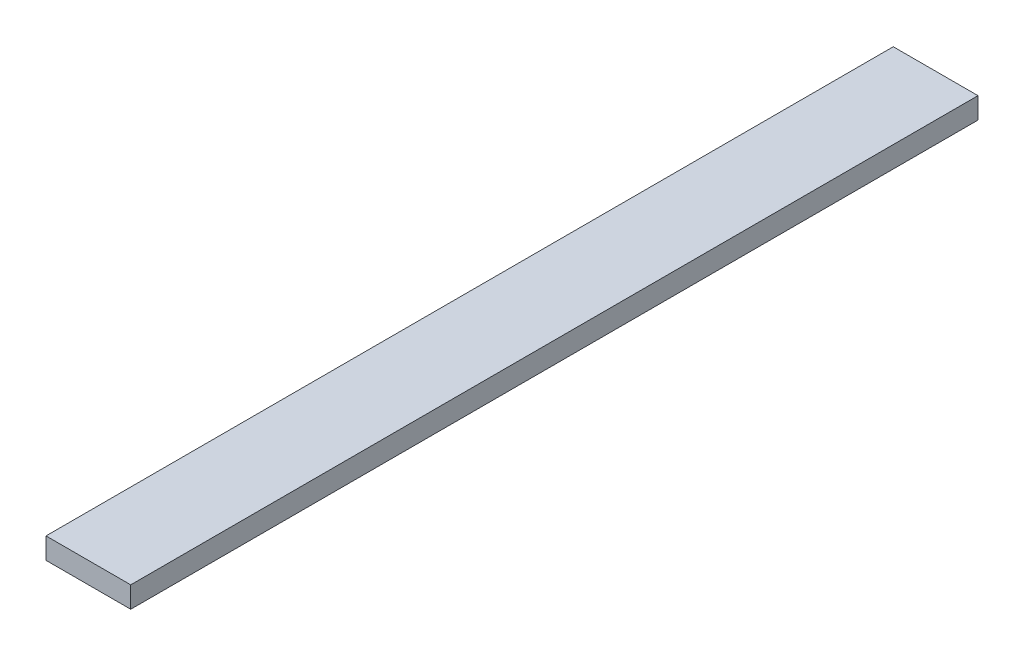
SolidWorks part; units mm, degrees
ref_plane "Front Plane" through (0, 0, 0) normal (0, 0, 1) x (1, 0, 0)
ref_plane "Top Plane" through (0, 0, 0) normal (0, 1, 0) x (1, 0, 0)
ref_plane "Right Plane" through (0, 0, 0) normal (1, 0, 0) x (0, 0, -1)
sketch "Sketch1" plane through (0, 0, 0) normal (0, 1, 0) x (1, 0, 0)
  line L1 (-3, -30) -> (3, -30)
  line L2 (-3, -30) -> (-3, 30)
  line L3 (-3, 30) -> (3, 30)
  line L4 (3, -30) -> (3, 30)
  line L5 (-3, -30) -> (3, 30) construction
  line L6 (-3, 30) -> (3, -30) construction
  point P0 (0, 0)
  dimension "D1" = 60
  dimension "D2" = 6
extrude "Boss-Extrude1" add sketch "Sketch1" along normal blind 1.5
